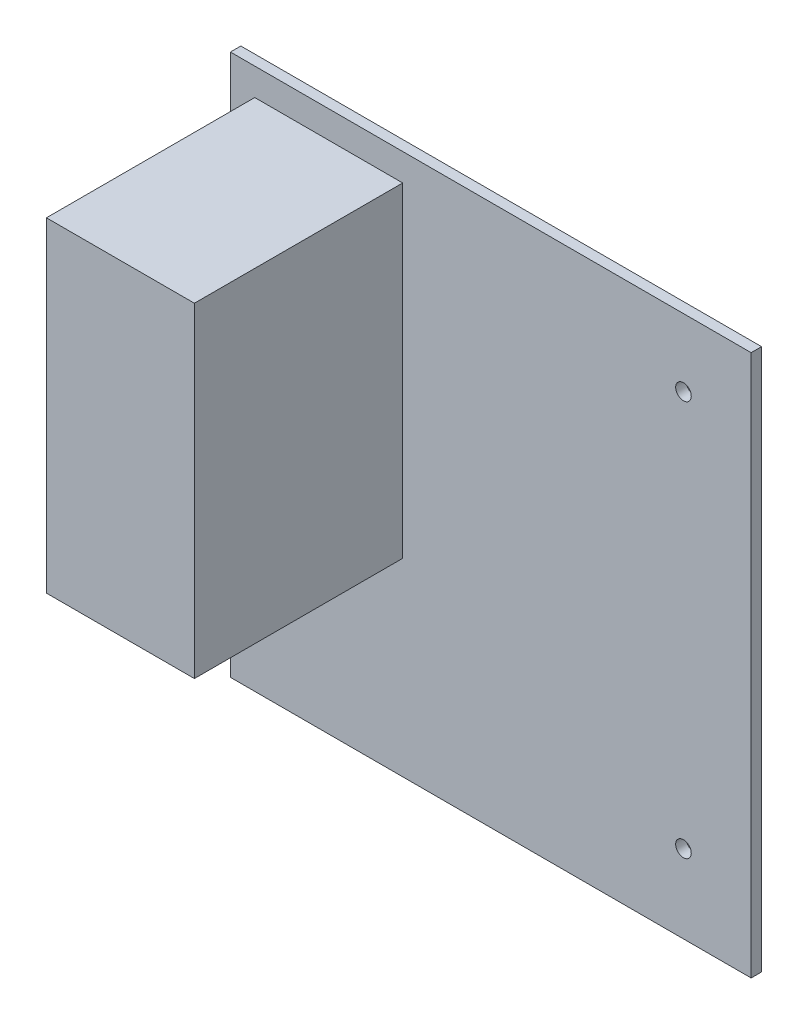
SolidWorks part; units mm, degrees
ref_plane "Front Plane" through (0, 0, 0) normal (0, 0, 1) x (1, 0, 0)
ref_plane "Top Plane" through (0, 0, 0) normal (0, 1, 0) x (1, 0, 0)
ref_plane "Right Plane" through (0, 0, 0) normal (1, 0, 0) x (0, 0, -1)
sketch "Sketch1" plane through (0, 0, 0) normal (0, 0, 1) x (1, 0, 0)
  line L1 (-50, 52) -> (50, 52)
  line L2 (-50, 52) -> (-50, -52)
  line L3 (-50, -52) -> (50, -52)
  line L4 (50, 52) -> (50, -52)
  line L5 (-50, 52) -> (50, -52) construction
  line L6 (-50, -52) -> (50, 52) construction
  point P0 (0, 0)
  dimension "D1" = 100
  dimension "D2" = 104
extrude "Boss-Extrude1" add sketch "Sketch1" along normal blind 2
sketch "Sketch2" plane through (0, 0, 2) normal (0, 0, 1) x (1, 0, 0)
  line L0 (-50, 52) -> (-50, -52) construction
  line L1 (-50, -52) -> (50, -52) construction
  circle A0 centre (-44, -37) radius 1.5
  circle A1 centre (37, -37) radius 1.5
  circle A2 centre (37, 39) radius 1.5
  dimension "D1" = 6
  dimension "D3" = 81
  dimension "D4" = 76
  dimension "D2" = 15
extrude "Cut-Extrude1" cut sketch "Sketch2" against normal blind 2
sketch "Sketch3" plane through (0, 0, 2) normal (0, 0, 1) x (1, 0, 0)
  line L1 (-45.3319, 46.7638) -> (-16.917, 46.7638)
  line L2 (-45.3319, 46.7638) -> (-45.3319, -15.6619)
  line L3 (-45.3319, -15.6619) -> (-16.917, -15.6619)
  line L4 (-16.917, 46.7638) -> (-16.917, -15.6619)
extrude "Boss-Extrude2" add sketch "Sketch3" along normal blind 40
